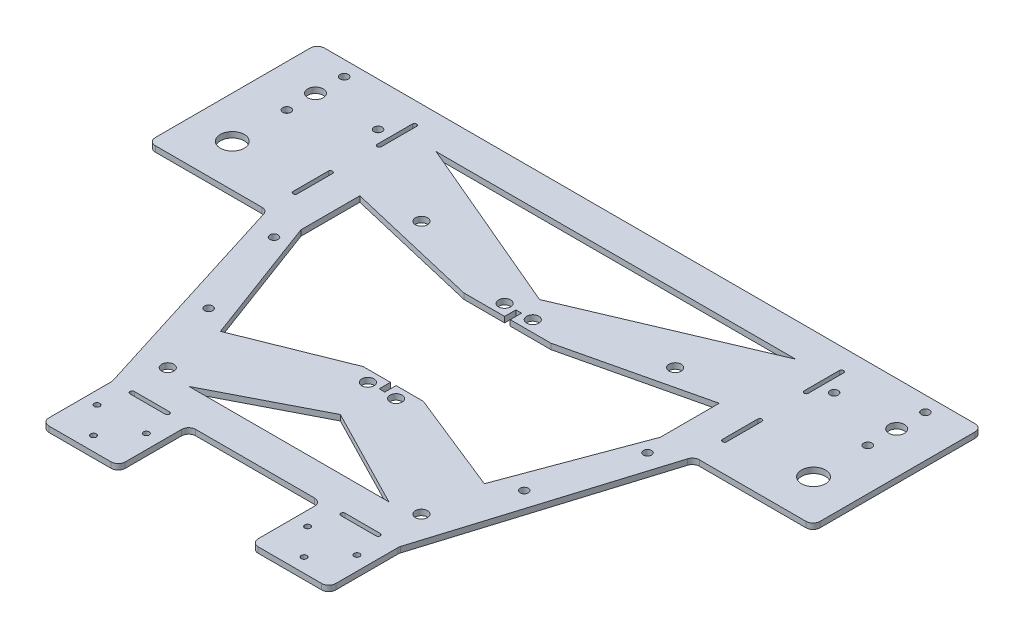
SolidWorks part; units mm, degrees
ref_plane "Front Plane" through (0, 0, 0) normal (0, 0, 1) x (1, 0, 0)
ref_plane "Top Plane" through (0, 0, 0) normal (0, 1, 0) x (1, 0, 0)
ref_plane "Right Plane" through (0, 0, 0) normal (1, 0, 0) x (0, 0, -1)
sketch "Sketch26" plane through (0, 0, 0) normal (0, 1, 0) x (1, 0, 0)
  line L0 (76.0133, 28.8235) -> (76.0133, 88.8235) construction
  line L1 (-63.5382, 76.8235) -> (64.0673, 76.8235)
  line L2 (0.2645, 93.3283) -> (0.2645, -99.0046) construction
  line L3 (21.3527, -51.1765) -> (-20.8236, -51.1765)
  line L4 (76.0133, 88.8235) -> (-76.0328, 88.8235)
  line L5 (-75.4842, 28.8235) -> (-75.4842, 88.8235) construction
  line L6 (115.6892, 88.8235) -> (76.0133, 88.8235)
  line L7 (-77.3206, 28.8235) -> (-115.1602, 28.8235)
  line L8 (-74.935, 27.0713) -> (-50.5239, -50.8121)
  line L9 (75.4699, 27.0594) -> (51.4834, -50.8168)
  line L10 (-117.6602, 31.3235) -> (-117.6602, 86.3235)
  line L11 (-115.1602, 88.8235) -> (-75.4842, 88.8235)
  line L12 (-75.91, 39.1911) -> (-75.91, 51.6911) construction
  line L13 (-76.66, 39.1911) -> (-76.66, 51.6911)
  line L14 (-75.16, 39.1911) -> (-75.16, 51.6911)
  line L15 (-75.4842, 81.0951) -> (-75.4842, 68.5951) construction
  line L16 (-74.7342, 81.0951) -> (-74.7342, 68.5951)
  line L17 (118.1892, 31.3235) -> (118.1892, 86.3235)
  line L18 (-76.2342, 81.0951) -> (-76.2342, 68.5951)
  line L19 (-46.5438, -16.6765) -> (-10.4029, -2.1765)
  line L20 (77.8592, 28.8235) -> (115.6892, 28.8235)
  line L21 (64.0133, 49.7097) -> (64.0133, 28.8235)
  line L22 (64.0133, 28.8235) -> (47.0729, -16.6765)
  line L23 (-63.4842, 28.8235) -> (-46.5438, -16.6765)
  line L24 (47.0729, -16.6765) -> (10.932, -2.1765)
  line L25 (15.7075, 38.3235) -> (64.0133, 49.7097)
  line L26 (-63.4842, 49.7097) -> (-63.4842, 28.8235)
  line L27 (1.2645, 42.3235) -> (1.2645, 38.3235)
  line L28 (1.2645, 42.3235) -> (-0.7355, 42.3235)
  line L29 (1.2645, 38.3235) -> (15.7075, 38.3235)
  line L30 (-0.7355, 42.3235) -> (-0.7355, 38.3235)
  line L31 (64.0673, 76.8235) -> (0.2645, 49.7097)
  line L32 (-0.7355, 38.3235) -> (-15.1784, 38.3235)
  line L33 (76.0133, 81.0951) -> (76.0133, 68.5951) construction
  line L34 (-15.1784, 38.3235) -> (-63.4842, 49.7097)
  line L35 (-63.5382, 76.8235) -> (0.2645, 49.7097)
  line L36 (1.2645, -2.1765) -> (10.932, -2.1765)
  line L37 (75.2633, 81.0951) -> (75.2633, 68.5951)
  line L38 (1.2645, -6.1765) -> (1.2645, -2.1765)
  line L39 (1.2645, -6.1765) -> (-0.7355, -6.1765)
  line L40 (-0.7355, -6.1765) -> (-0.7355, -2.1765)
  line L41 (-0.7355, -2.1765) -> (-10.4029, -2.1765)
  line L42 (-35.1832, -39.1765) -> (35.7123, -39.1765)
  line L43 (0.2645, -20.9512) -> (35.7123, -39.1765)
  line L44 (0.2645, -20.9512) -> (-35.1832, -39.1765)
  line L45 (51.3727, -51.5527) -> (51.3727, -73.6765)
  line L46 (48.8727, -76.1765) -> (26.3527, -76.1765)
  line L47 (76.7633, 81.0951) -> (76.7633, 68.5951)
  line L48 (76.4391, 39.1911) -> (76.4391, 51.6911) construction
  line L49 (77.1891, 39.1911) -> (77.1891, 51.6911)
  line L50 (75.6891, 39.1911) -> (75.6891, 51.6911)
  line L51 (23.8527, -73.6765) -> (23.8527, -53.6765)
  line L52 (37.6127, -76.1765) -> (37.6127, -51.1765) construction
  line L53 (51.3727, -76.1765) -> (51.3727, -51.1765)
  line L54 (23.8527, -51.1765) -> (23.8527, -76.1765)
  line L55 (-50.4095, -51.5599) -> (-50.4095, -73.6765)
  line L56 (-47.9095, -76.1765) -> (-25.8236, -76.1765)
  line L57 (-23.3236, -73.6765) -> (-23.3236, -53.6765)
  line L58 (31.4072, -51.1727) -> (43.9072, -51.1727) construction
  line L59 (31.4072, -50.4227) -> (43.9072, -50.4227)
  line L60 (31.4072, -51.9227) -> (43.9072, -51.9227)
  line L61 (-30.8781, -51.1727) -> (-43.3781, -51.1727) construction
  line L62 (-30.8781, -50.4227) -> (-43.3781, -50.4227)
  line L63 (-30.8781, -51.9227) -> (-43.3781, -51.9227)
  circle A0 centre (45.2645, 52.8235) radius 2.15
  circle A1 centre (45.2645, -37.1765) radius 2.15
  circle A2 centre (5.2645, 42.3235) radius 2.15
  circle A3 centre (5.2645, -6.1765) radius 2.15
  circle A4 centre (103.3673, 43.8235) radius 4.25
  arc A5 (118.1892, 31.3235) -> (115.6892, 28.8235) centre (115.6892, 31.3235) cw
  circle A6 centre (103.3673, 73.3235) radius 2.75
  circle A7 centre (103.3673, 83.5235) radius 1.45
  circle A8 centre (103.3133, 63.1237) radius 1.45
  circle A9 centre (81.1673, 73.3235) radius 1.45
  arc A10 (118.1892, 86.3235) -> (115.6892, 88.8235) centre (115.6892, 86.3235) ccw
  arc A11 (-117.6602, 86.3235) -> (-115.1602, 88.8235) centre (-115.1602, 86.3235) cw
  circle A12 centre (-80.6382, 73.3235) radius 1.45
  circle A13 centre (-102.7842, 63.1237) radius 1.45
  circle A14 centre (-102.8382, 83.5235) radius 1.45
  circle A15 centre (-102.8382, 73.3235) radius 2.75
  arc A16 (-117.6602, 31.3235) -> (-115.1602, 28.8235) centre (-115.1602, 31.3235) ccw
  arc A17 (75.2633, 81.0951) -> (76.7633, 81.0951) centre (76.0133, 81.0951) cw
  circle A18 centre (-102.8382, 43.8235) radius 4.25
  circle A19 centre (-4.7355, -6.1765) radius 2.15
  arc A20 (76.7633, 68.5951) -> (75.2633, 68.5951) centre (76.0133, 68.5951) cw
  arc A21 (77.1891, 39.1911) -> (75.6891, 39.1911) centre (76.4391, 39.1911) cw
  arc A22 (75.6891, 51.6911) -> (77.1891, 51.6911) centre (76.4391, 51.6911) cw
  circle A23 centre (-4.7355, 42.3235) radius 2.15
  circle A24 centre (-44.7355, -37.1765) radius 2.15
  circle A25 centre (-44.7355, 52.8235) radius 2.15
  arc A26 (-76.66, 39.1911) -> (-75.16, 39.1911) centre (-75.91, 39.1911) ccw
  arc A27 (-75.16, 51.6911) -> (-76.66, 51.6911) centre (-75.91, 51.6911) ccw
  arc A28 (-74.7342, 81.0951) -> (-76.2342, 81.0951) centre (-75.4842, 81.0951) ccw
  arc A29 (-76.2342, 68.5951) -> (-74.7342, 68.5951) centre (-75.4842, 68.5951) ccw
  circle A30 centre (28.8527, -61.1765) radius 1
  circle A31 centre (37.6127, -71.1765) radius 1
  circle A32 centre (46.3727, -61.1765) radius 1
  circle A33 centre (28.8527, -61.1765) radius 1
  circle A34 centre (46.3727, -61.1765) radius 1
  circle A35 centre (-28.3236, -61.1765) radius 1
  circle A36 centre (-45.8436, -61.1765) radius 1
  circle A37 centre (-37.0836, -71.1765) radius 1
  arc A38 (31.4072, -50.4227) -> (31.4072, -51.9227) centre (31.4072, -51.1727) ccw
  arc A39 (43.9072, -51.9227) -> (43.9072, -50.4227) centre (43.9072, -51.1727) ccw
  arc A40 (-30.8781, -50.4227) -> (-30.8781, -51.9227) centre (-30.8781, -51.1727) cw
  arc A41 (-43.3781, -51.9227) -> (-43.3781, -50.4227) centre (-43.3781, -51.1727) cw
  arc A42 (77.8592, 28.8235) -> (75.4699, 27.0594) centre (77.8592, 26.3235) ccw
  arc A43 (-74.935, 27.0713) -> (-77.3206, 28.8235) centre (-77.3206, 26.3235) ccw
  arc A44 (51.3727, -51.5527) -> (51.4834, -50.8168) centre (53.8727, -51.5527) cw
  arc A45 (21.3527, -51.1765) -> (23.8527, -53.6765) centre (21.3527, -53.6765) cw
  arc A46 (-20.8236, -51.1765) -> (-23.3236, -53.6765) centre (-20.8236, -53.6765) ccw
  arc A47 (-50.4095, -51.5599) -> (-50.5239, -50.8121) centre (-52.9095, -51.5599) ccw
  arc A48 (-23.3236, -73.6765) -> (-25.8236, -76.1765) centre (-25.8236, -73.6765) cw
  arc A49 (-47.9095, -76.1765) -> (-50.4095, -73.6765) centre (-47.9095, -73.6765) cw
  circle A50 centre (66.5151, 21.7665) radius 1.45
  circle A51 centre (56.2618, -11.698) radius 1.45
  circle A52 centre (-55.7328, -11.698) radius 1.45
  circle A53 centre (-65.9861, 21.7665) radius 1.45
  arc A54 (48.8727, -76.1765) -> (51.3727, -73.6765) centre (48.8727, -73.6765) ccw
  arc A55 (26.3527, -76.1765) -> (23.8527, -73.6765) centre (26.3527, -73.6765) cw
  circle A56 centre (0.2645, 7.8235) radius 1.4516
  point P60 (-75.91, 45.4411)
  point P63 (76.0133, 74.8451)
  point P71 (76.4391, 45.4411)
  point P77 (-75.4842, 74.8451)
  point P99 (0.2645, 42.3235)
  point P107 (0.2645, -6.1765)
  point P112 (0.2645, -39.1765)
  point P136 (37.6572, -51.1727)
  point P143 (-37.1281, -51.1727)
  point P162 (-23.3236, -51.1765)
  point P167 (-23.3236, -76.1765)
  dimension "D6" = 4.3
  dimension "D13" = 8.5
  dimension "D14" = 2.9
  dimension "D15" = 2.9
  dimension "D16" = 2.9
  dimension "D10" = 2.5
  dimension "D21" = 2.5
  dimension "D3" = 45
  dimension "D7" = 4.3
  dimension "D8" = 5.5
  dimension "D22" = 45
  dimension "D4" = 48.5
  dimension "D11" = 4.3
  dimension "D24" = 4.3
  dimension "D28" = 5
  dimension "D36" = 20
  dimension "D37" = 2.5
  dimension "D38" = 2.9
  dimension "D41" = 2.9
  dimension "D40" = 2.5
  dimension "D5" = 90
  dimension "D12" = 15
  dimension "D17" = 10.2
  dimension "D18" = 10.2
  dimension "D19" = 22.2
  dimension "D20" = 29.5
  dimension "D9" = 40
  dimension "D23" = 40
  dimension "D25" = 36
  dimension "D26" = 45
  dimension "D27" = 12
  dimension "D29" = 12
  dimension "D30" = 12
  dimension "D31" = 1
  dimension "D32" = 4
  dimension "D33" = 27.52
  dimension "D34" = 25
  dimension "D35" = 10
  dimension "D39" = 7
  dimension "D42" = 35
  dimension "D43" = 14
  dimension "D44" = 4
  dimension "D45" = 4
  dimension "D46" = 4
extrude "Boss-Extrude4" add sketch "Sketch26" along normal blind 2
